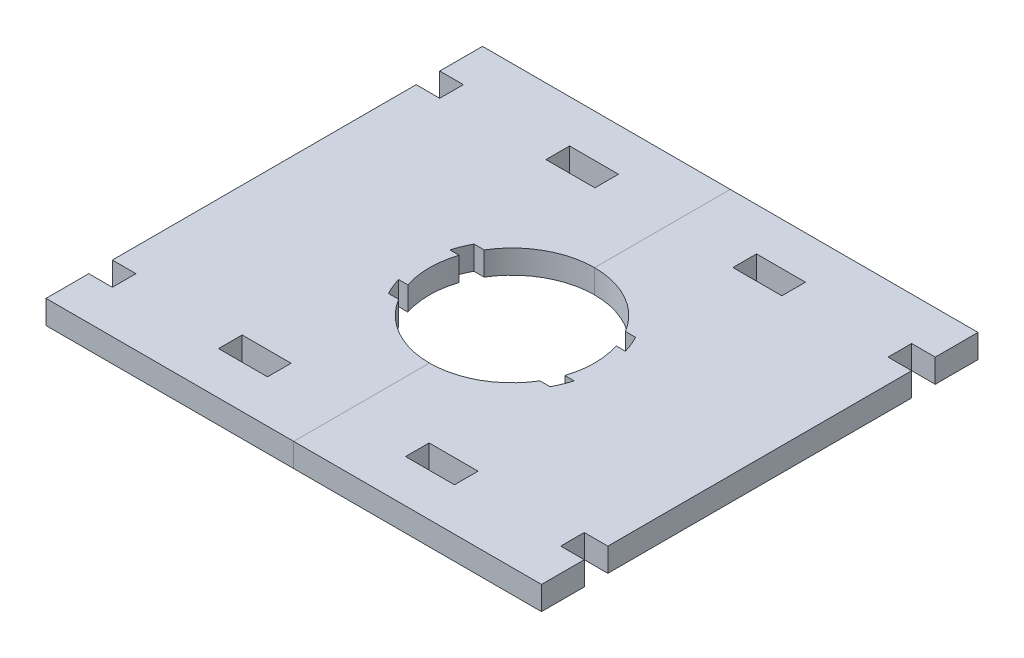
SolidWorks part; units mm, degrees
ref_plane "Front Plane" through (0, 0, 0) normal (0, 0, 1) x (1, 0, 0)
ref_plane "Top Plane" through (0, 0, 0) normal (0, 1, 0) x (1, 0, 0)
ref_plane "Right Plane" through (0, 0, 0) normal (1, 0, 0) x (0, 0, -1)
sketch "Sketch1" plane through (0, 0, 0) normal (0, 1, 0) x (1, 0, 0)
  line L0 (-15.5, 7.25) -> (-13.6999, 7.25) construction
  line L1 (-13.6999, -7.25) -> (-11.9765, -7.25)
  line L2 (-15.5, -7.25) -> (-15.5, -4.35) construction
  line L3 (-13.6999, 7.25) -> (-11.9765, 7.25)
  line L4 (15.5, 4.35) -> (15.5, 7.25) construction
  line L5 (-14.04, -6.5671) -> (-12.6813, -5.9316) construction
  line L6 (-14.04, 6.5671) -> (-12.6813, 5.9316) construction
  line L7 (-14.8771, -4.35) -> (-13.307, -4.35)
  line L8 (-15.5, -4.35) -> (-15.5, 0) construction
  line L9 (-14.8771, 4.35) -> (-13.307, 4.35)
  line L10 (15.5, 0) -> (15.5, 4.35) construction
  line L11 (-14.9234, -4.1882) -> (14.9234, 4.1882) construction
  line L12 (-14.9234, 4.1882) -> (14.9234, -4.1882) construction
  line L13 (-15.5, 7.25) -> (-14.04, 6.5671) construction
  line L14 (-15.5, 4.35) -> (-15.5, 7.25) construction
  line L15 (-15.5, 4.35) -> (-14.8771, 4.35) construction
  line L16 (-15.5, 4.35) -> (-14.9234, 4.1882) construction
  line L17 (-15.5, 0) -> (-15.5, 4.35) construction
  line L18 (-15.5, 0) -> (-15.5, 4.35) construction
  line L19 (-15.5, -4.35) -> (-15.5, 0) construction
  line L20 (-15.5, -4.35) -> (-14.9234, -4.1882) construction
  line L21 (-15.5, -4.35) -> (-14.8771, -4.35) construction
  line L22 (-15.5, -7.25) -> (-14.04, -6.5671) construction
  line L23 (-15.5, -7.25) -> (-13.6999, -7.25) construction
  line L24 (15.5, -7.25) -> (15.5, -4.35) construction
  line L25 (14.04, -6.5671) -> (15.5, -7.25) construction
  line L26 (13.6999, -7.25) -> (15.5, -7.25) construction
  line L27 (15.5, -4.35) -> (15.5, 0) construction
  line L28 (15.5, -4.35) -> (15.5, 0) construction
  line L29 (15.5, 0) -> (15.5, 4.35) construction
  line L30 (14.9234, 4.1882) -> (15.5, 4.35) construction
  line L31 (14.8771, 4.35) -> (15.5, 4.35) construction
  line L32 (13.6999, 7.25) -> (15.5, 7.25) construction
  line L33 (14.9234, -4.1882) -> (15.5, -4.35) construction
  line L34 (14.8771, -4.35) -> (15.5, -4.35) construction
  line L35 (-11.9765, 7.25) -> (11.9765, 7.25) construction
  line L36 (11.9765, 7.25) -> (13.6999, 7.25)
  line L37 (-9.3, 4.35) -> (9.3, 4.35) construction
  line L38 (13.307, 4.35) -> (14.8771, 4.35)
  line L39 (-12.6813, 5.9316) -> (-9.3, 4.35) construction
  line L40 (-9.3, 4.35) -> (9.3, -4.35) construction
  line L41 (-13.307, 4.35) -> (-9.3, 4.35) construction
  line L42 (-11.9765, -7.25) -> (11.9765, -7.25) construction
  line L43 (11.9765, -7.25) -> (13.6999, -7.25)
  line L44 (-9.3, -4.35) -> (9.3, -4.35) construction
  line L45 (13.307, -4.35) -> (14.8771, -4.35)
  line L46 (-12.6813, -5.9316) -> (-9.3, -4.35) construction
  line L47 (-9.3, -4.35) -> (9.3, 4.35) construction
  line L48 (-13.307, -4.35) -> (-9.3, -4.35) construction
  line L49 (9.3, -4.35) -> (13.307, -4.35) construction
  line L50 (9.3, -4.35) -> (12.6813, -5.9316) construction
  line L51 (12.6813, -5.9316) -> (14.04, -6.5671) construction
  line L52 (9.3, 4.35) -> (13.307, 4.35) construction
  line L53 (9.3, 4.35) -> (12.6813, 5.9316) construction
  line L54 (12.6813, 5.9316) -> (15.5, 7.25) construction
  arc A0 (-13.307, 4.35) -> (-13.307, -4.35) centre (0, 0) ccw
  arc A1 (-13.6999, 7.25) -> (-14.9234, 4.1882) centre (0, 0) ccw
  arc A2 (13.6999, 7.25) -> (-13.6999, 7.25) centre (0, 0) ccw construction
  arc A3 (-13.6999, -7.25) -> (13.6999, -7.25) centre (0, 0) ccw construction
  arc A4 (13.6999, -7.25) -> (14.9234, -4.1882) centre (0, 0) ccw
  arc A5 (15.5, 0) -> (14.9234, 4.1882) centre (0, 0) ccw construction
  arc A6 (14.9234, 4.1882) -> (13.6999, 7.25) centre (0, 0) ccw
  arc A7 (14.9234, -4.1882) -> (15.5, 0) centre (0, 0) ccw construction
  arc A8 (-14.9234, 4.1882) -> (-15.5, 0) centre (0, 0) ccw construction
  arc A9 (-14.9234, -4.1882) -> (-13.6999, -7.25) centre (0, 0) ccw
  arc A10 (-15.5, 0) -> (-14.9234, -4.1882) centre (0, 0) ccw construction
  arc A11 (-11.9765, 7.25) -> (-12.6813, 5.9316) centre (0, 0) ccw construction
  arc A12 (-12.6813, 5.9316) -> (-13.307, 4.35) centre (0, 0) ccw construction
  arc A13 (-12.6813, -5.9316) -> (-11.9765, -7.25) centre (0, 0) ccw construction
  arc A14 (-11.9765, -7.25) -> (11.9765, -7.25) centre (0, 0) ccw
  arc A15 (-13.307, -4.35) -> (-12.6813, -5.9316) centre (0, 0) ccw construction
  arc A16 (12.6813, -5.9316) -> (13.307, -4.35) centre (0, 0) ccw construction
  arc A17 (13.307, -4.35) -> (-11.9765, 7.25) centre (0, 0) ccw
  arc A18 (11.9765, -7.25) -> (12.6813, -5.9316) centre (0, 0) ccw construction
  dimension "D1" = 28
  dimension "D2" = 31
  dimension "D3" = 14.5
  dimension "D4" = 8.7
sketch "Sketch2" plane through (0, 0, 0) normal (0, 1, 0) x (1, 0, 0)
  line L0 (13.307, -4.35) -> (14.8771, -4.35) construction
  line L1 (-13.6999, 7.25) -> (-11.9765, 7.25) construction
  line L2 (-14.8771, -4.35) -> (-13.307, -4.35) construction
  line L3 (-14.8771, 4.35) -> (-13.307, 4.35) construction
  line L4 (11.9765, -7.25) -> (13.6999, -7.25) construction
  line L5 (-13.6999, -7.25) -> (-11.9765, -7.25) construction
  line L6 (11.9765, 7.25) -> (13.6999, 7.25) construction
  line L7 (13.307, 4.35) -> (14.8771, 4.35) construction
  line L8 (13.307, -4.35) -> (14.8771, -4.35)
  line L9 (-13.6999, 7.25) -> (-11.9765, 7.25)
  line L10 (-14.8771, -4.35) -> (-13.307, -4.35)
  line L11 (-14.8771, 4.35) -> (-13.307, 4.35)
  line L12 (11.9765, -7.25) -> (13.6999, -7.25)
  line L13 (-13.6999, -7.25) -> (-11.9765, -7.25)
  line L14 (11.9765, 7.25) -> (13.6999, 7.25)
  line L15 (13.307, 4.35) -> (14.8771, 4.35)
  line L17 (-42, -37) -> (42, -37)
  line L18 (-42, -37) -> (-42, 37)
  line L19 (-42, 37) -> (42, 37)
  line L20 (42, -37) -> (42, 37)
  line L21 (-42, -37) -> (42, 37) construction
  line L22 (-42, 37) -> (42, -37) construction
  arc A0 (13.307, -4.35) -> (-11.9765, 7.25) centre (0, 0) ccw construction
  arc A1 (-13.6999, 7.25) -> (-14.9234, 4.1882) centre (0, 0) ccw construction
  arc A2 (-13.307, 4.35) -> (-13.307, -4.35) centre (0, 0) ccw construction
  arc A3 (13.6999, -7.25) -> (14.9234, -4.1882) centre (0, 0) ccw construction
  arc A4 (-11.9765, -7.25) -> (11.9765, -7.25) centre (0, 0) ccw construction
  arc A5 (-14.9234, -4.1882) -> (-13.6999, -7.25) centre (0, 0) ccw construction
  arc A6 (14.9234, 4.1882) -> (13.6999, 7.25) centre (0, 0) ccw construction
  arc A7 (13.307, -4.35) -> (-11.9765, 7.25) centre (0, 0) ccw
  arc A8 (-13.6999, 7.25) -> (-14.9234, 4.1882) centre (0, 0) ccw
  arc A9 (-13.307, 4.35) -> (-13.307, -4.35) centre (0, 0) ccw
  arc A10 (13.6999, -7.25) -> (14.9234, -4.1882) centre (0, 0) ccw
  arc A11 (-11.9765, -7.25) -> (11.9765, -7.25) centre (0, 0) ccw
  arc A12 (-14.9234, -4.1882) -> (-13.6999, -7.25) centre (0, 0) ccw
  arc A13 (14.9234, 4.1882) -> (13.6999, 7.25) centre (0, 0) ccw
  dimension "D1" = 84
  dimension "D2" = 74
extrude "Boss-Extrude1" add sketch "Sketch2" along normal blind 4
split "Split1" trim tools "Right Plane" bodies to split 101 resulting bodies 102 103
sketch "Sketch4" plane through (0, 4, 0) normal (0, 1, 0) x (1, 0, 0)
  line L0 (0, -18.5) -> (42, -18.5) construction
  line L2 (42, -37) -> (42, 37) construction
  line L3 (0, -18.5) -> (0, -37) construction
  line L4 (-42, -37) -> (-42, 37) construction
  line L5 (-20, -29.75) -> (-11.7, -29.75)
  line L6 (-20, -29.75) -> (-20, -25.75)
  line L7 (-20, -25.75) -> (-11.7, -25.75)
  line L8 (-11.7, -29.75) -> (-11.7, -25.75)
  line L9 (-20, -29.75) -> (-11.7, -25.75) construction
  line L10 (-20, -25.75) -> (-11.7, -29.75) construction
  line L11 (-42, -29.75) -> (-38, -29.75)
  line L12 (-42, -29.75) -> (-42, -25.75)
  line L13 (-42, -25.75) -> (-38, -25.75)
  line L14 (-38, -29.75) -> (-38, -25.75)
  line L15 (-42, -29.75) -> (-38, -25.75) construction
  line L16 (-42, -25.75) -> (-38, -29.75) construction
  line L17 (0, 0) -> (0, -37) construction
  line L18 (-14.9234, 4.1882) -> (14.9234, -4.1882) construction
  line L33 (42, -25.75) -> (38, -29.75) construction
  line L34 (42, -29.75) -> (38, -25.75) construction
  line L35 (20, -25.75) -> (11.7, -29.75) construction
  line L36 (20, -29.75) -> (11.7, -25.75) construction
  line L45 (38, -29.75) -> (38, -25.75)
  line L46 (42, -25.75) -> (38, -25.75)
  line L47 (42, -29.75) -> (42, -25.75)
  line L48 (42, -29.75) -> (38, -29.75)
  line L49 (11.7, -29.75) -> (11.7, -25.75)
  line L50 (20, -25.75) -> (11.7, -25.75)
  line L51 (20, -29.75) -> (20, -25.75)
  line L52 (20, -29.75) -> (11.7, -29.75)
  line L53 (-2.2, 0) -> (2.2, 0) construction
  line L54 (20, 29.75) -> (11.7, 25.75) construction
  line L55 (20, 25.75) -> (11.7, 29.75) construction
  line L56 (42, 29.75) -> (38, 25.75) construction
  line L57 (42, 25.75) -> (38, 29.75) construction
  line L58 (20, 29.75) -> (11.7, 29.75)
  line L59 (20, 29.75) -> (20, 25.75)
  line L60 (20, 25.75) -> (11.7, 25.75)
  line L61 (11.7, 29.75) -> (11.7, 25.75)
  line L62 (42, 29.75) -> (38, 29.75)
  line L63 (42, 29.75) -> (42, 25.75)
  line L64 (42, 25.75) -> (38, 25.75)
  line L65 (38, 29.75) -> (38, 25.75)
  line L82 (-42, 25.75) -> (-38, 29.75) construction
  line L83 (-42, 29.75) -> (-38, 25.75) construction
  line L84 (-20, 25.75) -> (-11.7, 29.75) construction
  line L85 (-20, 29.75) -> (-11.7, 25.75) construction
  line L94 (-38, 29.75) -> (-38, 25.75)
  line L95 (-42, 25.75) -> (-38, 25.75)
  line L96 (-42, 29.75) -> (-42, 25.75)
  line L97 (-42, 29.75) -> (-38, 29.75)
  line L98 (-11.7, 29.75) -> (-11.7, 25.75)
  line L99 (-20, 25.75) -> (-11.7, 25.75)
  line L100 (-20, 29.75) -> (-20, 25.75)
  line L101 (-20, 29.75) -> (-11.7, 29.75)
  point P6 (-15.85, -27.75)
  point P14 (0, -27.75)
  point P15 (-40, -27.75)
  point P53 (40, -27.75)
  point P54 (15.85, -27.75)
  point P65 (15.85, 27.75)
  point P66 (40, 27.75)
  point P95 (-40, 27.75)
  point P96 (-15.85, 27.75)
  dimension "D1" = 4
  dimension "D2" = 8.3
  dimension "D3" = 20
  dimension "D4" = 4
extrude "Cut-Extrude2" cut sketch "Sketch4" against normal through all both
equation "\"m3_hole\"= 3.5"
equation "\"m3_washer\"= 7.3"
equation "\"m3_nut\"= 5.3"
equation "\"guide_width\"= 10.0"
equation "\"guide_length\"= 65.0"
equation "\"guide_tab_length\" = 10.0"
equation "\"guide_tab_width\" = 9.0"
equation "\"guide_thickness\" = 12.0"
equation "\"grinder_od\"= 52.0"
equation "\"grinder_id\"= 45.5"
equation "\"grinder_adjust_od\" = 58.0"
equation "\"funnel_width_from_adjust_ring\" = 13.0"
equation "\"drill_contact_diameter_small\" = 24.0"
equation "\"drill_contact_diameter_medium\" = 28.0"
equation "\"drill_contact_diameter_large\" = 39.0"
equation "\"drill_contact_diameter_tab\" = 31.0"
equation "\"drill_contact_ow_tab\" = 14.5"
equation "\"drill_contact_iw_tab\" = 8.7"
equation "\"drill_contact_small_height\" = 15.5"
equation "\"drill_contact_large_height\" = 34.5"
equation "\"D1@Sketch1\"=\"drill_contact_diameter_medium\""
equation "\"D2@Sketch1\"=\"drill_contact_diameter_tab\""
equation "\"D3@Sketch1\"=\"drill_contact_ow_tab\""
equation "\"D1@Sketch2\"=\"grinder_od\"+\"guide_thickness\"+20"
equation "\"D2@Sketch2\"=\"grinder_od\"+\"guide_thickness\"+\"guide_tab_length\""
equation "\"plywood_thickness\" = 3.85"
equation "\"D4@Sketch1\"=\"drill_contact_iw_tab\""
equation "\"plywood_peg_length\" = 40"
equation "\"plywood_peg_width\" = 8.3"
equation "\"D3@Sketch4\"=\"plywood_peg_length\"/2"
equation "\"D2@Sketch4\"=\"plywood_peg_width\""
